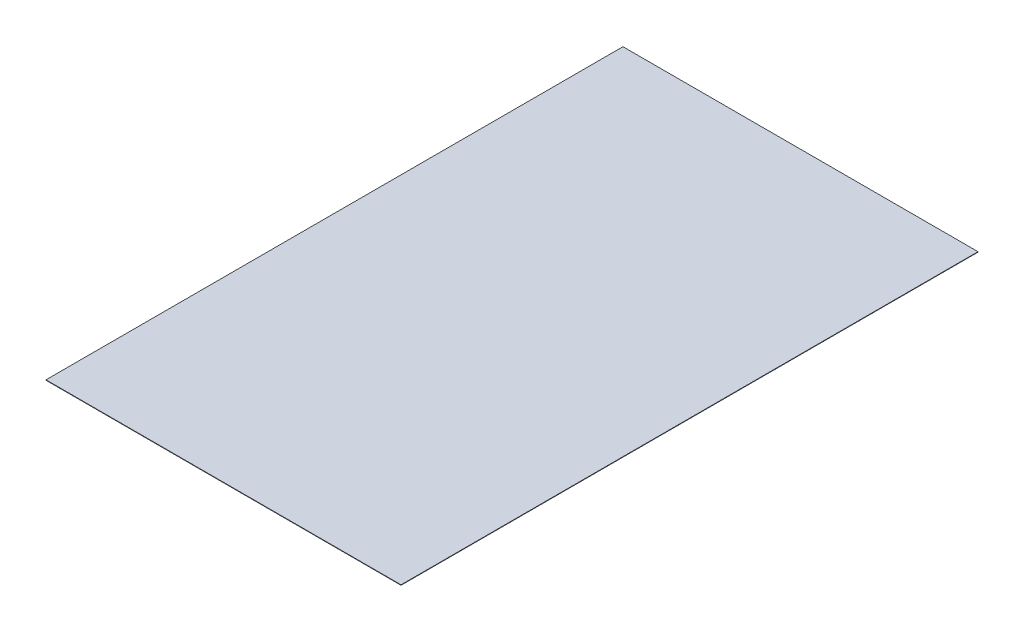
SolidWorks part; units mm, degrees
ref_plane "前视基准面" through (0, 0, 0) normal (0, 0, 1) x (1, 0, 0)
ref_plane "上视基准面" through (0, 0, 0) normal (0, 1, 0) x (1, 0, 0)
ref_plane "右视基准面" through (0, 0, 0) normal (1, 0, 0) x (0, 0, -1)
sketch "草图1" plane through (0, 0, 0) normal (0, 1, 0) x (1, 0, 0)
  line L1 (0, 0) -> (400, 0)
  line L2 (0, 0) -> (0, 650)
  line L3 (0, 650) -> (400, 650)
  line L4 (400, 0) -> (400, 650)
  dimension "D1" = 650
  dimension "D2" = 400
extrude "凸台-拉伸1" add sketch "草图1" along normal blind 0.5
